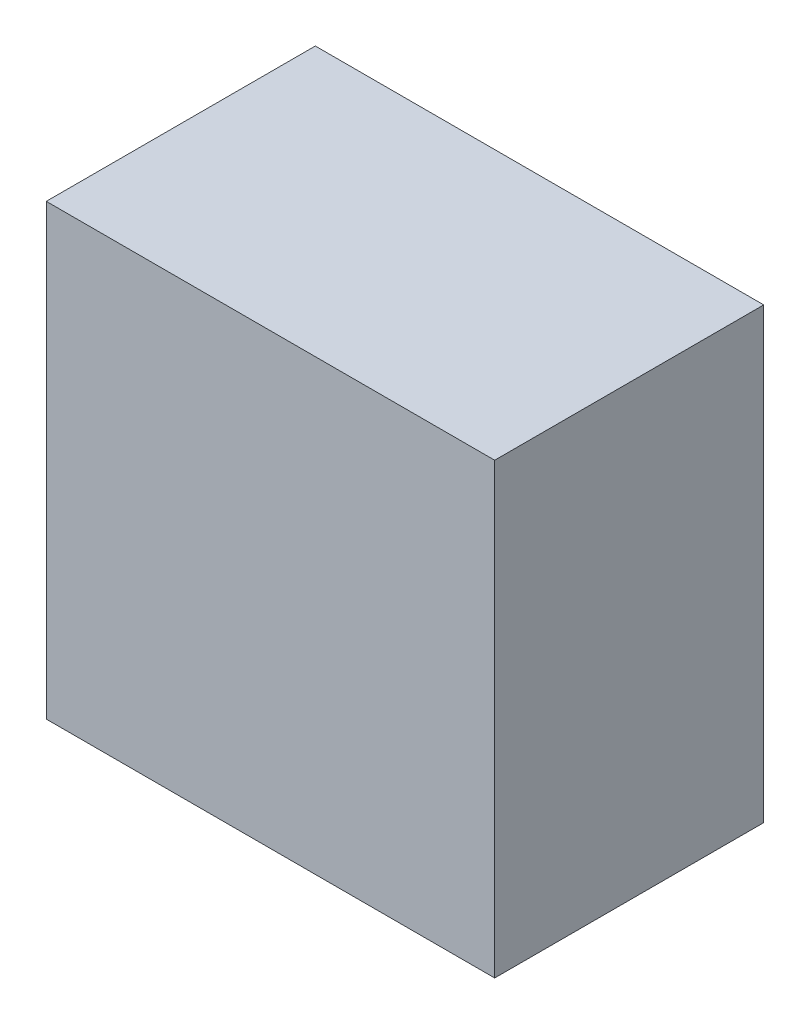
SolidWorks part; units mm, degrees
ref_plane "Front" through (0, 0, 0) normal (0, 0, 1) x (1, 0, 0)
ref_plane "Top" through (0, 0, 0) normal (0, 1, 0) x (1, 0, 0)
ref_plane "Right" through (0, 0, 0) normal (1, 0, 0) x (0, 0, -1)
sketch "Sketch1" plane through (0, 0, 0) normal (0, 0, 1) x (1, 0, 0)
  line L1 (-25, -25) -> (25, -25)
  line L2 (-25, -25) -> (-25, 25)
  line L3 (-25, 25) -> (25, 25)
  line L4 (25, -25) -> (25, 25)
  line L5 (-25, -25) -> (25, 25) construction
  line L6 (-25, 25) -> (25, -25) construction
  point P0 (0, 0)
  dimension "D1" = 50
  dimension "D2" = 50
extrude "Boss-Extrude1" add sketch "Sketch1" along normal blind 30
